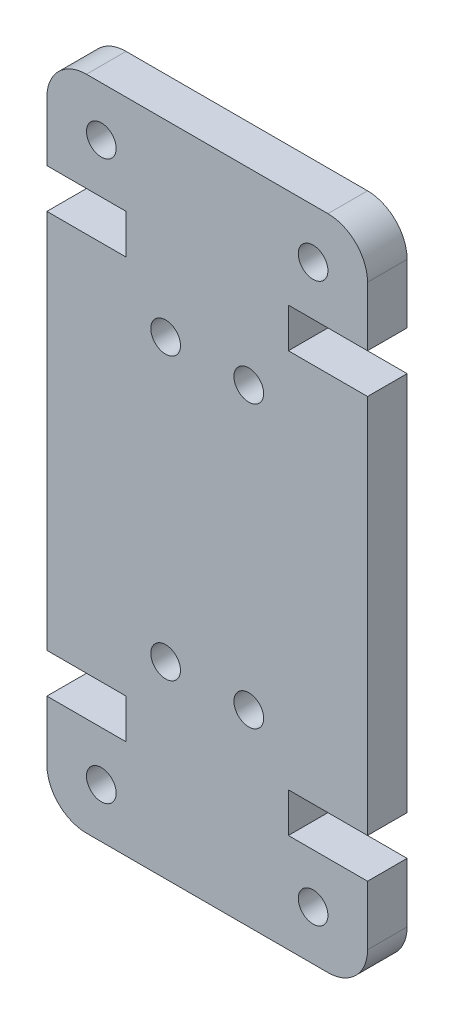
SolidWorks part; units mm, degrees
ref_plane "Front Plane" through (0, 0, 0) normal (0, 0, 1) x (1, 0, 0)
ref_plane "Top Plane" through (0, 0, 0) normal (0, 1, 0) x (1, 0, 0)
ref_plane "Right Plane" through (0, 0, 0) normal (1, 0, 0) x (0, 0, -1)
sketch "Sketch1" plane through (0, 0, 0) normal (0, 0, 1) x (1, 0, 0)
  line L0 (0, 26.21) -> (0, 7)
  line L1 (16.2, 2) -> (16.2, 5)
  line L2 (12.2, 5) -> (16.2, 5)
  line L3 (2, 0) -> (14.2, 0)
  line L4 (16.2, 7) -> (12.2, 7)
  line L5 (12.2, 7) -> (12.2, 5)
  line L6 (16.2, 26.21) -> (16.2, 7)
  line L7 (4, 7) -> (4, 5)
  line L8 (0, 31.21) -> (0, 28.21)
  line L9 (4, 28.21) -> (0, 28.21)
  line L10 (0, 7) -> (4, 7)
  line L11 (0, 26.21) -> (4, 26.21)
  line L12 (4, 5) -> (0, 5)
  line L13 (4, 26.21) -> (4, 28.21)
  line L14 (12.2, 26.21) -> (12.2, 28.21)
  line L15 (16.2, 26.21) -> (12.2, 26.21)
  line L16 (0, 2) -> (0, 5)
  line L17 (2, 33.21) -> (14.2, 33.21)
  line L18 (12.2, 28.21) -> (16.2, 28.21)
  line L19 (16.2, 31.21) -> (16.2, 28.21)
  line L20 (0, 16.605) -> (16.2, 16.605) construction
  line L21 (8.1, 33.21) -> (8.1, 0) construction
  circle A0 centre (13.45, 2.5) radius 0.75
  circle A1 centre (10.2, 9.5) radius 0.75
  arc A2 (16.2, 2) -> (14.2, 0) centre (14.2, 2) cw
  circle A3 centre (2.75, 30.71) radius 0.75
  circle A4 centre (6, 23.71) radius 0.75
  arc A5 (0, 2) -> (2, 0) centre (2, 2) ccw
  arc A6 (0, 31.21) -> (2, 33.21) centre (2, 31.21) cw
  circle A7 centre (6, 9.5) radius 0.75
  arc A8 (16.2, 31.21) -> (14.2, 33.21) centre (14.2, 31.21) ccw
  circle A9 centre (2.75, 2.5) radius 0.75
  circle A10 centre (10.2, 23.71) radius 0.75
  circle A11 centre (13.45, 30.71) radius 0.75
  point P15 (8.1, 16.605)
  dimension "D1" = 1.5
  dimension "D2" = 2
  dimension "D3" = 2.75
  dimension "D4" = 6
  dimension "D5" = 8.1
  dimension "D6" = 2.5
  dimension "D7" = 5
  dimension "D9" = 9.5
  dimension "D10" = 16.605
extrude "Boss-Extrude1" add sketch "Sketch1" along normal blind 2
equation "\"D5@Sketch1\"= \"fingerWidth@parametersSketch@prostheticParameters.SLDPRT\" / 2'PIP width"
equation "\"D10@Sketch1\"= ( \"HL@parametersSketch@prostheticParameters.SLDPRT\" * 0.266 - 12 - 4 ) / 2 'PIP length - Sil. sht PIP-Sil Sht MIP"
